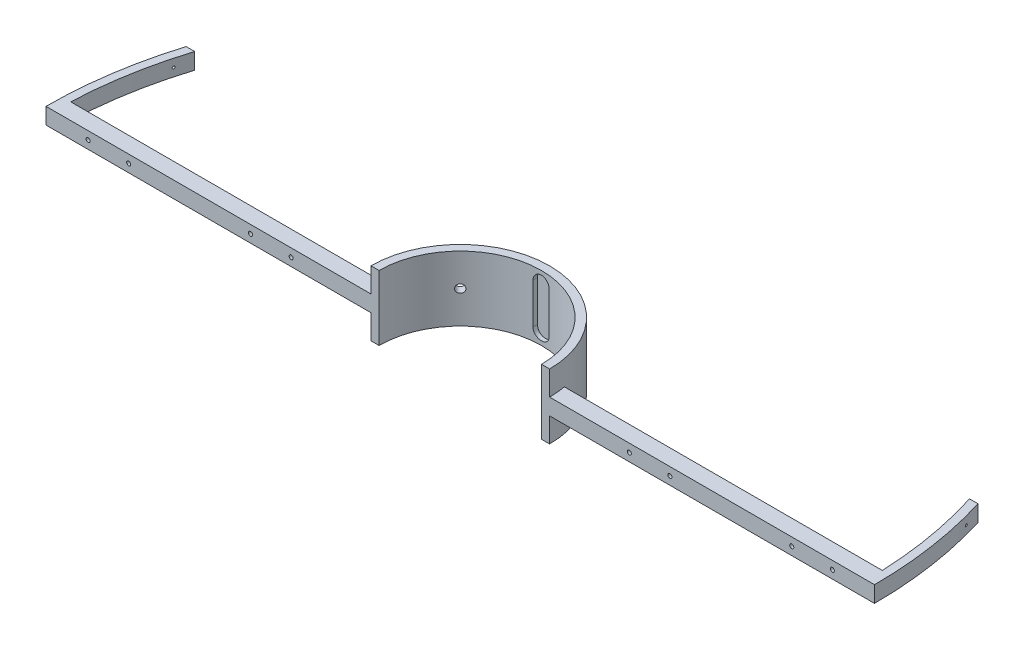
SolidWorks part; units mm, degrees
ref_plane "Front Plane" through (0, 0, 0) normal (0, 0, 1) x (1, 0, 0)
ref_plane "Top Plane" through (0, 0, 0) normal (0, 1, 0) x (1, 0, 0)
ref_plane "Right Plane" through (0, 0, 0) normal (1, 0, 0) x (0, 0, -1)
sketch "Sketch1" plane through (0, 0, 0) normal (0, 1, 0) x (1, 0, 0)
  line L0 (-110, 0) -> (-100, 0)
  line L1 (100, 0) -> (110, 0)
  arc A0 (100, 0) -> (-100, 0) centre (0, 0) ccw
  arc A1 (-110, 0) -> (110, 0) centre (0, 0) cw
  point P6 (0, 100)
  point P7 (-77.7817, 77.7817)
  point P8 (77.7817, 77.7817)
  dimension "D1" = 100
  dimension "D2" = 110
  dimension "D3" = 10
extrude "Boss-Extrude1" add sketch "Sketch1" along normal blind 80
ref_plane "Plane1" through (100, 80, 0) normal (-1, 0, 0) x (0, 0, 1)
sketch "Sketch2" plane through (100, 80, 0) normal (-1, 0, 0) x (0, 0, 1)
  line L0 (0, -40) -> (-20, -40)
  line L1 (0, 0) -> (0, -80) construction
  line L2 (-20, -40) -> (-20, -30)
  line L3 (-20, -30) -> (0, -30)
  line L4 (0, -30) -> (0, -50)
  line L5 (0, -50) -> (-20, -50)
  line L6 (-20, -50) -> (-20, -40)
  dimension "D1" = 20
  dimension "D2" = 20
  dimension "D3" = 10
extrude "Boss-Extrude2" add sketch "Sketch2" against normal blind 400 contours L3 L4 L0 L2 | L5 L6 L0 L4
ref_plane "Plane2" through (-100, 80, 0) normal (1, 0, 0) x (0, 0, -1)
sketch "Sketch3" plane through (-100, 80, 0) normal (1, 0, 0) x (0, 0, -1)
  line L1 (0, -50) -> (20, -50)
  line L2 (0, -50) -> (0, -30)
  line L3 (0, -30) -> (20, -30)
  line L4 (20, -50) -> (20, -30)
extrude "Boss-Extrude3" add sketch "Sketch3" against normal blind 400
ref_plane "Plane3" through (0, 50, 0) normal (0, 1, 0) x (1, 0, 0)
sketch "Sketch5" plane through (0, 50, 0) normal (0, 1, 0) x (1, 0, 0)
  line L0 (500, 0) -> (510, 0)
  line L3 (476.9696, 150) -> (487.4423, 150)
  line L5 (0, 0) -> (500, 0)
  line L6 (0, 0) -> (0, 200)
  line L7 (-476.9696, 150) -> (-487.4423, 150)
  line L8 (-500, 0) -> (-510, 0)
  arc A0 (500, 0) -> (476.9696, 150) centre (0, 0) ccw
  arc A1 (510, 0) -> (487.4423, 150) centre (0, 0) ccw
  arc A2 (-510, 0) -> (-487.4423, 150) centre (0, 0) cw
  arc A3 (-500, 0) -> (-476.9696, 150) centre (0, 0) cw
  dimension "D1" = 150
  dimension "D2" = 500
  dimension "D3" = 10
  dimension "D4" = 200
extrude "Boss-Extrude4" add sketch "Sketch5" against normal blind 20 contours L0 A1 L3 A0
sketch "Sketch7" plane through (0, 50, 0) normal (0, 1, 0) x (1, 0, 0)
  line L0 (0, 0) -> (-500, 0)
  line L1 (-500, 0) -> (-510, 0)
  line L2 (-487.4423, 150) -> (-476.9696, 150)
  arc A0 (-500, 0) -> (-476.9696, 150) centre (0, 0) cw
  arc A1 (-510, 0) -> (-487.4423, 150) centre (0, 0) cw
  dimension "D1" = 10
  dimension "D2" = 150
extrude "Boss-Extrude5" add sketch "Sketch7" against normal blind 20 contours A1 L1 A0 L2
ref_plane "Plane4" through (0, 0, -100) normal (0, 0, 1) x (1, 0, 0)
ref_plane "Plane5" through (0, 0, -20) normal (0, 0, -1) x (-1, 0, 0)
sketch "Sketch10" plane through (0, 0, -20) normal (0, 0, -1) x (-1, 0, 0)
  line L0 (108.1665, 30) -> (108.1665, 50) construction
  line L1 (-108.1665, 30) -> (-108.1665, 50) construction
  circle A0 centre (-258.1665, 40) radius 2.5
  circle A1 centre (-408.1665, 40) radius 2.5
  circle A2 centre (258.1665, 40) radius 2.5
  circle A3 centre (408.1665, 40) radius 2.5
  circle A4 centre (-458.1665, 40) radius 2.5
  circle A5 centre (-208.1665, 40) radius 2.5
  circle A6 centre (208.1665, 40) radius 2.5
  circle A7 centre (458.1665, 40) radius 2.5
  point P0 (-258.1665, 40)
  point P1 (-408.1665, 40)
  point P2 (108.1665, 40)
  point P3 (258.1665, 40)
  point P6 (408.1665, 40)
  point P9 (-108.1665, 40)
  point P18 (458.1665, 40)
  point P19 (208.1665, 40)
  point P20 (-208.1665, 40)
  point P21 (-458.1665, 40)
  dimension "D5" = 50
  dimension "D9" = 5
  dimension "D10" = 5
  dimension "D11" = 5
  dimension "D12" = 5
  dimension "D13" = 5
  dimension "D14" = 5
  dimension "D15" = 5
  dimension "D16" = 5
  dimension "D1" = 150
  dimension "D2" = 300
  dimension "D3" = 150
  dimension "D4" = 300
  dimension "D6" = 50
  dimension "D7" = 50
  dimension "D8" = 50
extrude "Cut-Extrude1" cut sketch "Sketch10" against normal blind 20
ref_plane "Plane6" through (-77.7817, 0, -77.7817) normal (-0.7071, 0, -0.7071) x (-0.7071, 0, 0.7071)
sketch "Sketch11" plane through (-77.7817, 0, -77.7817) normal (-0.7071, 0, -0.7071) x (-0.7071, 0, 0.7071)
  line L0 (0, 0) -> (0, 80)
  line L1 (77.7817, 80) -> (-110, 80) construction
  circle A0 centre (0, 40) radius 5
extrude "Cut-Extrude3" cut sketch "Sketch11" against normal blind 20 contours A0
ref_plane "Plane7" through (77.7817, 0, -77.7817) normal (0.7071, 0, -0.7071) x (-0.7071, 0, -0.7071)
sketch "Sketch12" plane through (77.7817, 0, -77.7817) normal (0.7071, 0, -0.7071) x (-0.7071, 0, -0.7071)
  line L0 (0, 0) -> (0, 80)
  line L1 (110, 80) -> (-77.7817, 80) construction
  circle A0 centre (0, 40) radius 5
  dimension "D1" = 10
extrude "Cut-Extrude4" cut sketch "Sketch12" against normal blind 20 contours A0
ref_plane "Plane9" through (0, 0, -90) normal (0, 0, 1) x (1, 0, 0)
sketch "Sketch15" plane through (0, 0, -90) normal (0, 0, 1) x (1, 0, 0)
  line L0 (0, 0) -> (0, 80)
  line L1 (100, 80) -> (-100, 80) construction
  line L3 (-10, 65) -> (10, 65)
  line L4 (-10, 65) -> (-10, 15)
  line L5 (-10, 15) -> (10, 15)
  line L6 (10, 65) -> (10, 15)
  arc A0 (10, 65) -> (-10, 65) centre (0, 65) ccw
  arc A1 (-10, 15) -> (10, 15) centre (0, 15) ccw
  point P9 (0, 15)
  dimension "D4" = 10
  dimension "D1" = 50
  dimension "D2" = 20
  dimension "D3" = 15
extrude "Cut-Extrude7" cut sketch "Sketch15" against normal blind 15 contours L0 A1 L5 | L5 A1 L0 | L6 L3 L0 L5 | L4 L5 L0 L3 | L3 A0 L0 | L0 A0 L3
ref_plane "Plane10" through (-510, 30, 0) normal (-1, 0, 0) x (0, 0, 1)
sketch "Sketch16" plane through (-510, 30, 0) normal (-1, 0, 0) x (0, 0, 1)
  line L0 (-150, 0) -> (-150, 20) construction
  line L1 (0, 20) -> (-150, 20) construction
  circle A0 centre (-130, 10) radius 1.5
  point P0 (-130, 10)
  dimension "D3" = 3
  dimension "D1" = 20
  dimension "D2" = 10
extrude "Cut-Extrude8" cut sketch "Sketch16" against normal blind 50
ref_plane "Plane11" through (510, 30, 0) normal (1, 0, 0) x (0, 0, -1)
sketch "Sketch17" plane through (510, 30, 0) normal (1, 0, 0) x (0, 0, -1)
  line L0 (150, 0) -> (150, 20) construction
  line L1 (150, 20) -> (0, 20) construction
  circle A0 centre (130, 10) radius 1.5
  point P0 (130, 10)
  dimension "D3" = 3
  dimension "D1" = 20
  dimension "D2" = 10
extrude "Cut-Extrude9" cut sketch "Sketch17" against normal blind 50
